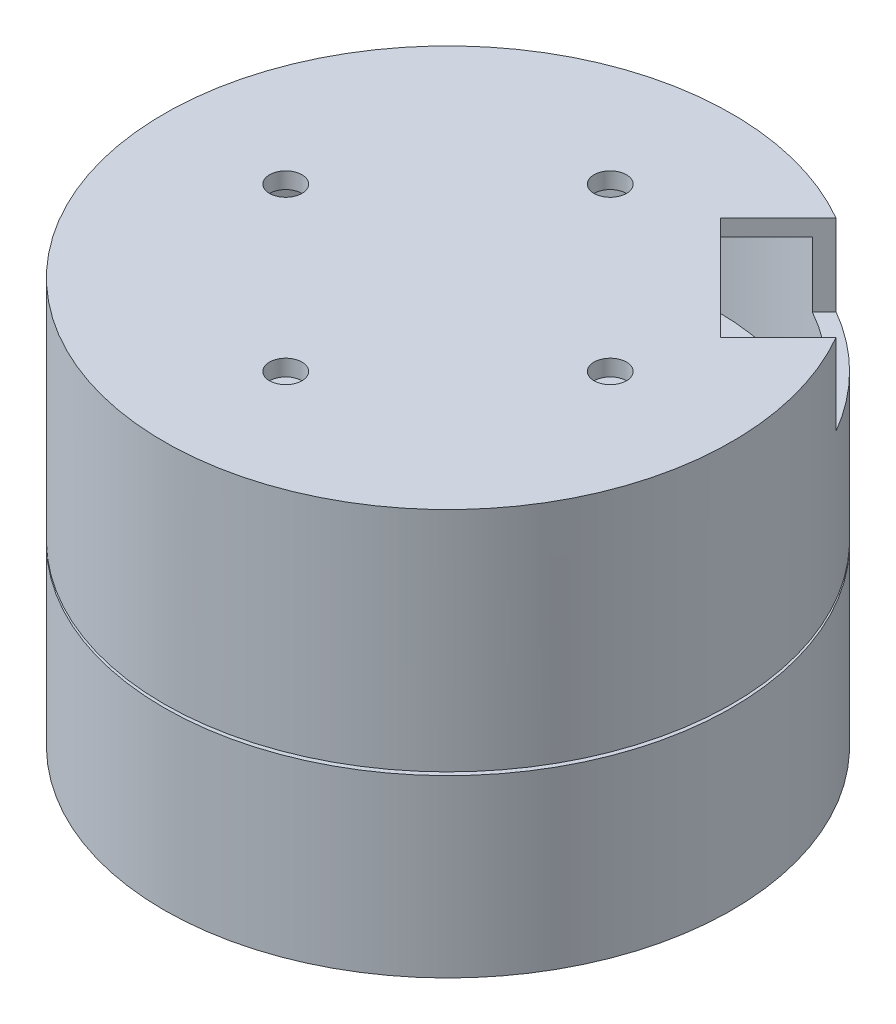
SolidWorks part; units mm, degrees
ref_plane "Front Plane" through (0, 0, 0) normal (0, 0, 1) x (1, 0, 0)
ref_plane "Top Plane" through (0, 0, 0) normal (0, 1, 0) x (1, 0, 0)
ref_plane "Right Plane" through (0, 0, 0) normal (1, 0, 0) x (0, 0, -1)
sketch "Sketch1" plane through (0, 0, 0) normal (0, 1, 0) x (1, 0, 0)
  circle A0 centre (0, 0) radius 17.5
  dimension "D1" = 35
extrude "Boss-Extrude1" add sketch "Sketch1" along normal blind 15
sketch "Sketch2" plane through (0, 15, 0) normal (0, 1, 0) x (1, 0, 0)
  line L1 (7.3, 0) -> (3.65, 6.322)
  line L2 (3.65, 6.322) -> (-3.65, 6.322)
  line L3 (-3.65, 6.322) -> (-7.3, 0)
  line L4 (-7.3, 0) -> (-3.65, -6.322)
  line L5 (-3.65, -6.322) -> (3.65, -6.322)
  line L6 (3.65, -6.322) -> (7.3, 0)
  circle A0 centre (0, 0) radius 6.322 construction
  circle A1 centre (0, 0) radius 7.5 construction
  dimension "D1" = 15
  dimension "D2" = 7.3
extrude "Boss-Extrude2" add sketch "Sketch2" along normal blind 2
sketch "Sketch3" plane through (0, 0, 0) normal (0, -1, 0) x (1, 0, 0)
  circle A0 centre (0, 0) radius 3.25
  dimension "D1" = 6.5
extrude "Cut-Extrude1" cut sketch "Sketch3" against normal up to next
sketch "Sketch4" plane through (0, 0, 0) normal (0, -1, 0) x (1, 0, 0)
  circle A0 centre (0, 9.5) radius 1
  dimension "D1" = 2
  dimension "D2" = 9.5
extrude "Cut-Extrude2" cut sketch "Sketch4" against normal blind 5
pattern_circular "CirPattern1" count 4 over 360 about axis through (0, 0, 0) along (0, 1, 0) of "Cut-Extrude2"
sketch "Sketch5" plane through (0, 15, 0) normal (0, 1, 0) x (1, 0, 0)
  circle A0 centre (0, 14.5) radius 1
  dimension "D1" = 2
  dimension "D2" = 14.5
extrude "Cut-Extrude3" cut sketch "Sketch5" against normal blind 2
pattern_circular "CirPattern2" count 4 over 360 about axis through (0, 0, 0) along (0, 1, 0) of "Cut-Extrude3"
sketch "Sketch6" plane through (0, 15, 0) normal (0, 1, 0) x (1, 0, 0)
  line L0 (7.3, 0) -> (3.65, 6.322) construction
  line L1 (7.3, 0) -> (3.65, 6.322)
  line L2 (3.65, 6.322) -> (-3.65, 6.322)
  line L3 (-3.65, 6.322) -> (-7.3, 0)
  line L4 (-7.3, 0) -> (-3.65, -6.322)
  line L5 (-3.65, -6.322) -> (3.65, -6.322)
  line L6 (3.65, -6.322) -> (7.3, 0)
  circle A0 centre (0, 0) radius 7.5
  circle A1 centre (0, 0) radius 6.322 construction
  dimension "D1" = 15
extrude "Cut-Extrude4" cut sketch "Sketch6" against normal blind 5
sketch "Sketch7" plane through (0, 15, 0) normal (0, 1, 0) x (1, 0, 0)
  circle A0 centre (0, 0) radius 17.5
  circle A1 centre (0, 0) radius 12.5
  circle A2 centre (0, 0) radius 17.5 construction
  dimension "D1" = 5
extrude "Cut-Extrude6" cut sketch "Sketch7" against normal blind 0.2 from offset 4 offset against normal yes
fillet "Fillet1" radius 2 6 edges at (-3.65, 13.5, 6.322) (-7.3, 13.5, 0) (-3.65, 13.5, -6.322) (3.65, 13.5, -6.322) (7.3, 13.5, 0) (3.65, 13.5, 6.322)
sketch "Sketch8" plane through (0, 15, 0) normal (0, 1, 0) x (1, 0, 0)
  line L0 (0, -1000) -> (0, 49000) construction
  line L1 (0, 0) -> (11.6673, 11.6673) construction
  line L2 (8.043, 14.407) -> (5.2146, 11.5785)
  line L3 (5.2146, 11.5785) -> (11.5785, 5.2146)
  line L4 (11.5785, 5.2146) -> (14.407, 8.043)
  circle A0 centre (0, 0) radius 16.5 construction
  circle A1 centre (0, 0) radius 17.5 construction
  arc A2 (14.407, 8.043) -> (8.043, 14.407) centre (0, 0) ccw
  point P10 (8.3965, 8.3965)
  dimension "D1" = 1
  dimension "D2" = 45
  dimension "D3" = 4
  dimension "D4" = 9
extrude "Cut-Extrude7" cut sketch "Sketch8" against normal blind 3
sketch "Sketch9" plane through (0, 15, 0) normal (0, 1, 0) x (1, 0, 0)
  circle A0 centre (0, 0) radius 17.5
  circle A1 centre (0, 0) radius 16.5
  circle A2 centre (0, 0) radius 17.5 construction
  dimension "D1" = 1
extrude "Boss-Extrude3" add sketch "Sketch9" along normal offset from surface (10 mm away) 25 up to face at (8.5, 0, 0)
sketch "Sketch10" plane through (0, 25, 0) normal (0, 1, 0) x (1, 0, 0)
  circle A0 centre (0, 0) radius 16.5
  circle A2 centre (0, 0) radius 16.5 construction
extrude "Boss-Extrude4" add sketch "Sketch10" against normal blind 1
sketch "Sketch11" plane through (0, 25, 0) normal (0, 1, 0) x (1, 0, 0)
  line L0 (5.2146, 11.5785) -> (11.5785, 5.2146)
  line L1 (11.5785, 5.2146) -> (15.1402, 8.7763)
  line L2 (5.2146, 11.5785) -> (8.7763, 15.1402)
  line L3 (8.043, 14.407) -> (5.2146, 11.5785) construction
  circle A0 centre (0, 0) radius 17.5 construction
  arc A1 (8.7763, 15.1402) -> (15.1402, 8.7763) centre (0, 0) cw
  point P8 (0, 0)
extrude "Cut-Extrude8" cut sketch "Sketch11" against normal blind 5
sketch "Sketch12" plane through (0, 25, 0) normal (0, 1, 0) x (1, 0, 0)
  circle A0 centre (0, 0) radius 10 construction
  circle A1 centre (0, 10) radius 1
  dimension "D1" = 20
  dimension "D2" = 2
extrude "Cut-Extrude9" cut sketch "Sketch12" against normal up to next (1 mm away)
pattern_circular "CirPattern3" count 4 over 360 about axis through (0, 0, 0) along (0, 1, 0) of "Cut-Extrude9"
equation "\"D2@Sketch2\"=\"D1@Sketch2\"/2-0.2"
